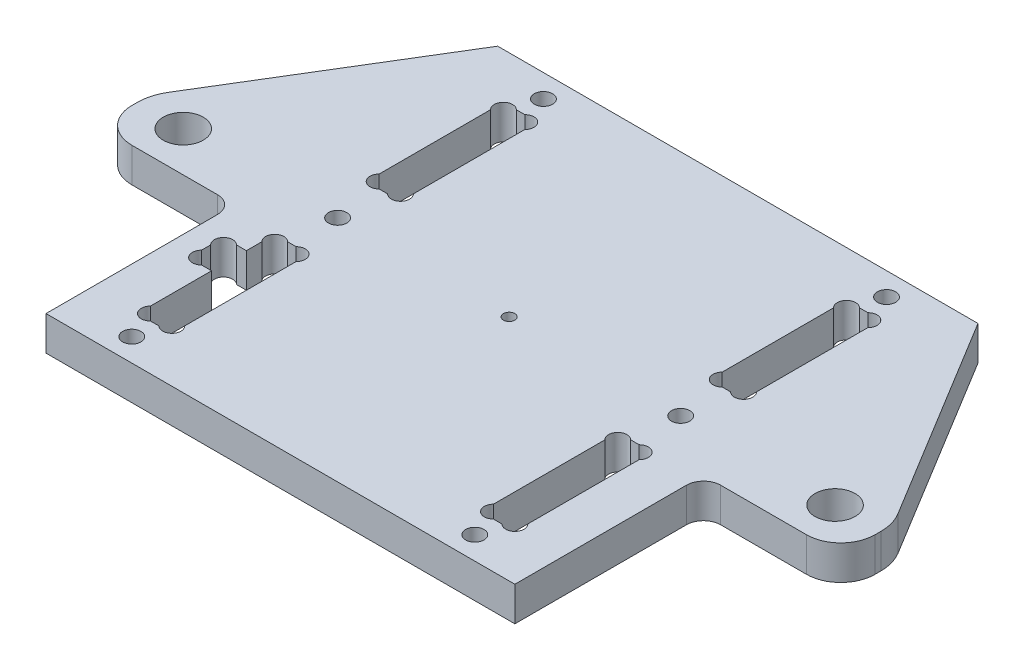
SolidWorks part; units mm, degrees
ref_plane "Plan de face" through (0, 0, 0) normal (0, 0, 1) x (1, 0, 0)
ref_plane "Plan de dessus" through (0, 0, 0) normal (0, 1, 0) x (1, 0, 0)
ref_plane "Plan de droite" through (0, 0, 0) normal (1, 0, 0) x (0, 0, -1)
sketch "Esquisse1" plane through (0, 0, 0) normal (0, 1, 0) x (1, 0, 0)
  line L0 (-116.9557, 0) -> (110.5569, 0) construction
  line L1 (0, -14.338) -> (0, 107.476) construction
  line L2 (-116.9557, 80) -> (110.5569, 80) construction
  line L3 (-65, 95.0623) -> (-65, -11.8265) construction
  line L4 (-33, -11.8265) -> (-33, 88.3991) construction
  line L5 (-111.2655, 40) -> (13.9471, 40) construction
  line L6 (-27, 84.3292) -> (-27, -7.5711) construction
  line L7 (-30, 43.1695) -> (-30, 8.6994) construction
  line L8 (-38.3779, 8) -> (-28.7848, 8) construction
  line L9 (-28.7848, 20) -> (-31.8686, 20) construction
  line L10 (-33, 50.2627) -> (-33, 69.7373)
  line L11 (-42.309, 32) -> (-29.8525, 32) construction
  line L12 (-27, 8) -> (-35.1739, 16.1739) construction
  line L13 (-33, 4) -> (-27, 4) construction
  line L14 (-30.7373, 32) -> (-29.2627, 32)
  line L15 (-33, 29.7373) -> (-33, 27.05)
  line L16 (-30.7373, 8) -> (-29.2627, 8)
  line L17 (-27, 29.7373) -> (-27, 10.2627)
  line L18 (-27, 50.2627) -> (-27, 69.7373)
  line L19 (-30.7373, 48) -> (-29.2627, 48)
  line L20 (-30.7373, 72) -> (-29.2627, 72)
  line L21 (42, 80) -> (63.8321, 44.162)
  line L22 (65, 39) -> (65, 40)
  line L23 (30.7373, 72) -> (29.2627, 72)
  line L24 (30.7373, 48) -> (29.2627, 48)
  line L25 (27, 50.2627) -> (27, 69.7373)
  line L26 (27, 29.7373) -> (27, 10.2627)
  line L27 (-57, 44.7413) -> (-57, 35.4436) construction
  line L28 (-63.8321, 44.162) -> (-42, 80) construction
  line L29 (30.7373, 8) -> (29.2627, 8)
  line L30 (-42, 80) -> (-63.8321, 44.162)
  line L31 (-65, 39) -> (-65, 40)
  line L32 (33, 29.7373) -> (33, 10.2627)
  line L33 (30.7373, 32) -> (29.2627, 32)
  line L34 (33, 50.2627) -> (33, 69.7373)
  line L35 (-42, 80) -> (42, 80)
  line L36 (41, 0) -> (-41, 0)
  line L37 (-74.9954, 33) -> (-10.3063, 33) construction
  line L38 (-41, 0) -> (-41, 30)
  line L39 (-59, 33) -> (-44, 33)
  line L40 (41, 0) -> (41, 30)
  line L41 (59, 33) -> (44, 33)
  line L42 (-43.5505, 24) -> (-18.6263, 24) construction
  line L43 (-69, -15.7297) -> (-69, 36.4985) construction
  line L44 (-45.5, 23.9637) -> (-45.5, -9.1324) construction
  line L45 (-41, -9.1324) -> (-41, 37.5974) construction
  line L46 (-31.1187, 20.95) -> (-38.9416, 20.95) construction
  line L47 (-31.1187, 27.05) -> (-38.9416, 27.05) construction
  line L48 (-37, 28.3928) -> (-37, 19.1751) construction
  line L49 (-37, 27.05) -> (-33.5922, 23.6422) construction
  line L50 (-33, 27.05) -> (-34.7373, 27.05)
  line L51 (-37, 24.7873) -> (-37, 23.2127)
  line L52 (-34.7373, 20.95) -> (-33, 20.95)
  line L53 (-33, 20.95) -> (-33, 10.2627)
  arc A0 (-29.2627, 8) -> (-27, 10.2627) centre (-28.1314, 9.1314) ccw
  arc A1 (-30.7373, 8) -> (-33, 10.2627) centre (-31.8686, 9.1314) cw
  arc A2 (-30.7373, 32) -> (-33, 29.7373) centre (-31.8686, 30.8686) ccw
  arc A3 (-29.2627, 32) -> (-27, 29.7373) centre (-28.1314, 30.8686) cw
  circle A4 centre (-30, 4) radius 1.6
  circle A5 centre (-30, 76) radius 1.6
  arc A6 (-29.2627, 72) -> (-27, 69.7373) centre (-28.1314, 70.8686) cw
  arc A7 (-30.7373, 72) -> (-33, 69.7373) centre (-31.8686, 70.8686) ccw
  arc A8 (-29.2627, 48) -> (-27, 50.2627) centre (-28.1314, 49.1314) ccw
  arc A9 (-30.7373, 48) -> (-33, 50.2627) centre (-31.8686, 49.1314) cw
  circle A10 centre (-30, 40) radius 1.6
  arc A11 (63.8321, 44.162) -> (65, 40) centre (57, 40) cw
  circle A12 centre (57, 40) radius 3.5
  circle A13 centre (30, 4) radius 1.6
  circle A14 centre (30, 40) radius 1.6
  arc A15 (30.7373, 48) -> (33, 50.2627) centre (31.8686, 49.1314) ccw
  arc A16 (-63.8321, 44.162) -> (-65, 40) centre (-57, 40) ccw
  circle A17 centre (-57, 40) radius 3.5
  arc A18 (29.2627, 48) -> (27, 50.2627) centre (28.1314, 49.1314) cw
  arc A19 (30.7373, 72) -> (33, 69.7373) centre (31.8686, 70.8686) cw
  arc A20 (29.2627, 72) -> (27, 69.7373) centre (28.1314, 70.8686) ccw
  circle A21 centre (30, 76) radius 1.6
  arc A22 (29.2627, 32) -> (27, 29.7373) centre (28.1314, 30.8686) ccw
  arc A23 (30.7373, 32) -> (33, 29.7373) centre (31.8686, 30.8686) cw
  arc A24 (30.7373, 8) -> (33, 10.2627) centre (31.8686, 9.1314) ccw
  arc A25 (29.2627, 8) -> (27, 10.2627) centre (28.1314, 9.1314) cw
  circle A26 centre (0, 40) radius 1
  arc A27 (-65, 39) -> (-59, 33) centre (-59, 39) ccw
  arc A28 (-44, 33) -> (-41, 30) centre (-44, 30) cw
  arc A29 (44, 33) -> (41, 30) centre (44, 30) ccw
  arc A30 (65, 39) -> (59, 33) centre (59, 39) cw
  arc A31 (-34.7373, 27.05) -> (-37, 24.7873) centre (-35.8686, 25.9186) ccw
  arc A32 (-34.7373, 20.95) -> (-37, 23.2127) centre (-35.8686, 22.0814) cw
  point P108 (-41, 33)
  point P110 (-65, 33)
  dimension "D8" = 8
  dimension "D10" = 3
  dimension "D3" = 6
  dimension "D1" = 6
  dimension "D2" = 3
  dimension "D4" = 24
  dimension "D5" = 12
  dimension "D6" = 4
  dimension "D7" = 45
  dimension "D9" = 8
  dimension "D11" = 36
  dimension "D12" = 23.5
  dimension "D13" = 8
  dimension "D14" = 24
  dimension "D15" = 3.05
  dimension "D16" = 6.1
  dimension "D17" = 4
  dimension "D18" = 45
extrude "Extrusion1" add sketch "Esquisse1" along normal blind 6
